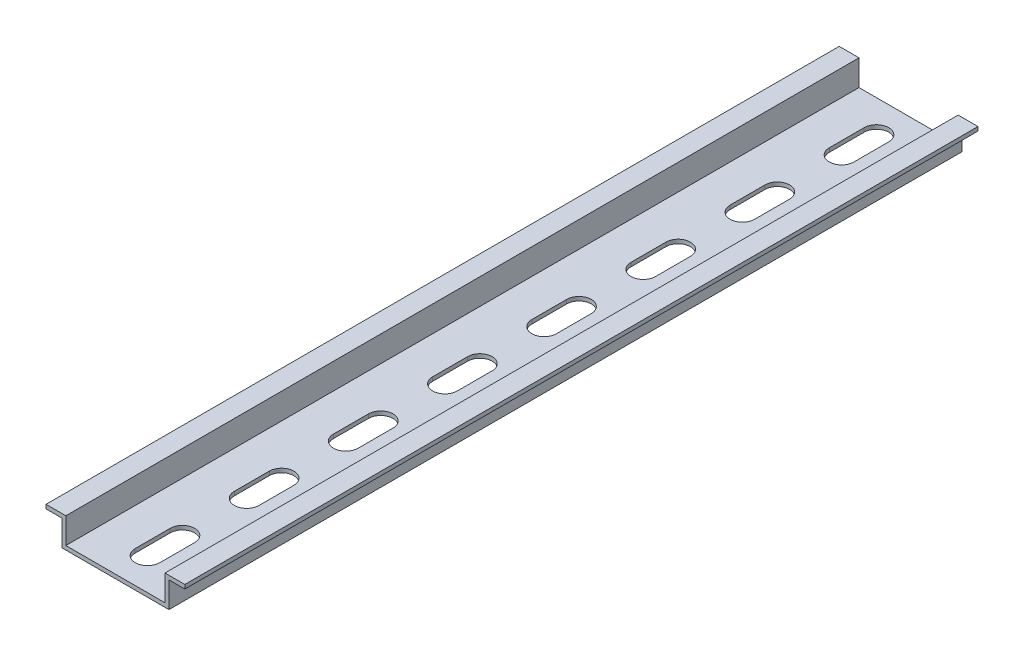
SolidWorks part; units mm, degrees
material "1060 Alloy"
ref_plane "Front Plane" through (0, 0, 0) normal (0, 0, 1) x (1, 0, 0)
ref_plane "Top Plane" through (0, 0, 0) normal (0, 1, 0) x (1, 0, 0)
ref_plane "Right Plane" through (0, 0, 0) normal (1, 0, 0) x (0, 0, -1)
sketch "Sketch1" plane through (0, 0, 0) normal (0, 0, 1) x (1, 0, 0)
  line L0 (0, 0) -> (13.5, 0)
  line L1 (13.5, 0) -> (13.5, 6.5)
  line L2 (13.5, 6.5) -> (17.5, 6.5)
  line L3 (17.5, 6.5) -> (17.5, 7.5)
  line L4 (17.5, 7.5) -> (12.5, 7.5)
  line L5 (12.5, 7.5) -> (12.5, 1)
  line L6 (12.5, 1) -> (0, 1)
  line L7 (0, 1) -> (0, 0)
  line L8 (13.5, 6.5) -> (12.5, 6.5) construction
  dimension "D1" = 1
  dimension "D2" = 13.5
  dimension "D3" = 6.5
  dimension "D4" = 4
extrude "Boss-Extrude1" add sketch "Sketch1" along normal blind 200
sketch "Sketch2" plane through (0, 0, 0) normal (0, 1, 0) x (1, 0, 0)
  line L0 (0, -8.1) -> (0, -16.9) construction
  line L1 (3.1, -8.1) -> (3.1, -16.9)
  line L2 (-3.1, -8.1) -> (-3.1, -16.9)
  line L3 (0, -200) -> (0, 0) construction
  arc A0 (3.1, -8.1) -> (-3.1, -8.1) centre (0, -8.1) ccw
  arc A1 (-3.1, -16.9) -> (3.1, -16.9) centre (0, -16.9) ccw
  point P2 (0, -12.5)
  point P7 (0, 0)
  point P10 (0, -16.7964)
  dimension "D2" = 3.1
  dimension "D1" = 8.8
  dimension "D3" = 12.5
extrude "Cut-Extrude1" cut sketch "Sketch2" along normal through all
pattern_linear "LPattern1" count 8 spacing 25 along (0, 0, 1) of "Cut-Extrude1"
mirror "Mirror2" about plane through (0, 0, 0) normal (1, 0, 0) of "LPattern1", "Cut-Extrude1", "Boss-Extrude1"
